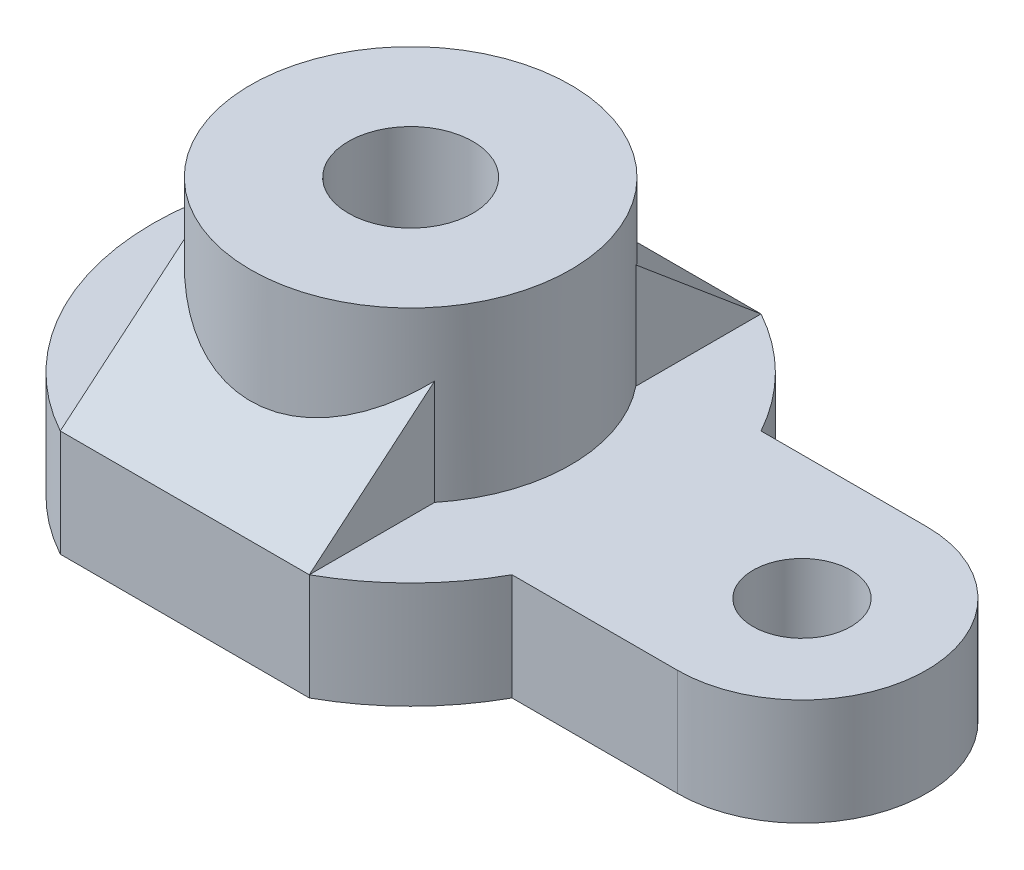
SolidWorks part; units mm, degrees
ref_plane "Front Plane" through (0, 0, 0) normal (0, 0, 1) x (1, 0, 0)
ref_plane "Top Plane" through (0, 0, 0) normal (0, 1, 0) x (1, 0, 0)
ref_plane "Right Plane" through (0, 0, 0) normal (1, 0, 0) x (0, 0, -1)
sketch "Sketch1" plane through (0, 0, 0) normal (0, 1, 0) x (1, 0, 0)
  line L0 (0, 0) -> (88, 0) construction
  line L1 (-28, -50.7937) -> (28, -50.7937)
  line L2 (-28, 50.7937) -> (28, 50.7937)
  line L3 (88, 28) -> (50.7937, 28)
  line L4 (88, -28) -> (50.7937, -28)
  circle A2 centre (88, 0) radius 11
  arc A3 (50.7937, 28) -> (28, 50.7937) centre (0, 0) ccw
  arc A4 (88, -28) -> (88, 28) centre (88, 0) ccw
  arc A5 (-28, 50.7937) -> (-28, -50.7937) centre (0, 0) ccw
  arc A6 (28, -50.7937) -> (50.7937, -28) centre (0, 0) ccw
  point P8 (-40.4403, 41.5762)
  point P12 (41.5447, 40.4726)
  point P13 (0, 0)
  dimension "D4" = 22
  dimension "D5" = 58
  dimension "D6" = 28
  dimension "D3" = 88
  dimension "D7" = 56
extrude "base" add sketch "Sketch1" along normal blind 24
sketch "Sketch2" plane through (0, 24, 0) normal (0, 1, 0) x (1, 0, 0)
  circle A0 centre (0, 0) radius 36
  circle A1 centre (0, 0) radius 14
  dimension "D1" = 72
  dimension "D2" = 28
extrude "top cylinder" add sketch "Sketch2" along normal blind 38
sketch3d "3DSketch1"
  line L0 (28, 24, 50.7937) -> (28, 0, 50.7937) construction
  line L1 (28, 24, -50.7937) -> (28, 0, -50.7937) construction
  line L2 (28, 24, 50.7937) -> (28, 47.6343, 22.6274)
  line L3 (28, 24, 50.7937) -> (28, 24, 22.6274)
  line L4 (28, 47.6343, 22.6274) -> (28, 24, 22.6274)
  line L5 (28, 24, 50.7937) -> (28, 24, -50.7937) construction
  line L6 (28, 24, 0) -> (28, 60.5105, 0) construction
  line L7 (28, 24, -50.7937) -> (28, 47.6343, -22.6274)
  line L8 (28, 47.6343, -22.6274) -> (28, 24, -22.6274)
  line L9 (28, 24, -50.7937) -> (28, 24, -22.6274)
  arc A0 (28, 24, 50.7937) -> (50.7937, 24, 28) centre (0, 24, 0) ccw construction
  circle A1 centre (0, 24, 0) radius 36 construction
  point P12 (0, 82, 0)
  point P13 (28, 24, 0)
  point P18 (0, 60, 0)
  dimension "D1" = 40
extrude "side arms" add sketch "3DSketch1" along direction (1, 0, 0) on the side against the normal blind 56 contours L3 L4 L2 | L7 L8 L9
